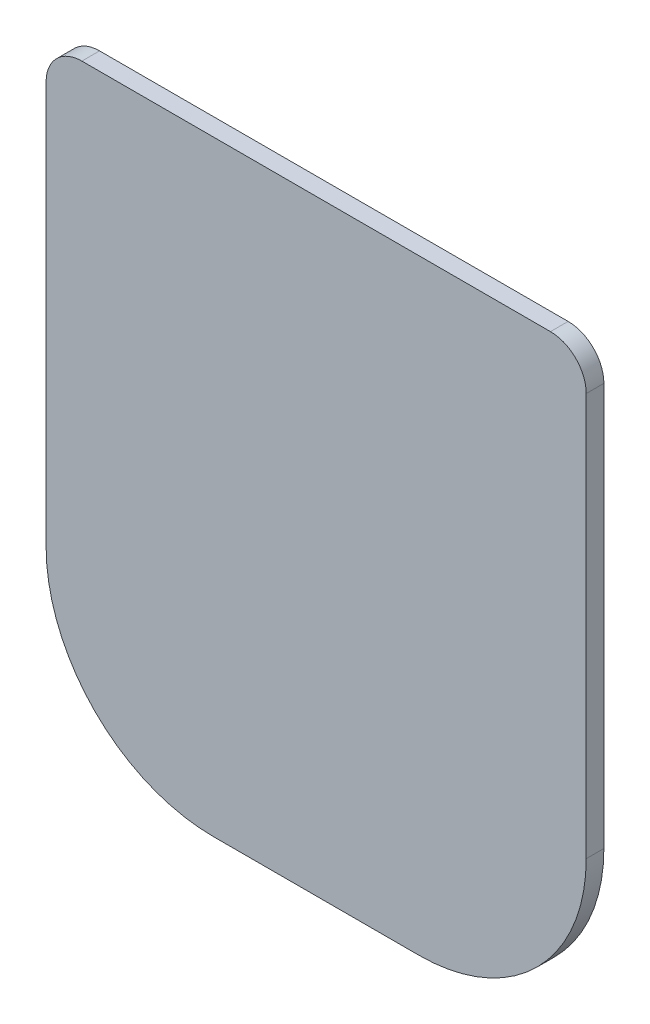
SolidWorks part; units mm, degrees
ref_plane "Front Plane" through (0, 0, 0) normal (0, 0, 1) x (1, 0, 0)
ref_plane "Top Plane" through (0, 0, 0) normal (0, 1, 0) x (1, 0, 0)
ref_plane "Right Plane" through (0, 0, 0) normal (1, 0, 0) x (0, 0, -1)
sketch "Sketch1" plane through (0, 0, 0) normal (0, 0, 1) x (1, 0, 0)
  line L0 (70, -39.19) -> (70, 58.81) construction
  line L1 (-25, -84.19) -> (-0.5, -84.19) construction
  line L2 (0.5, -84.19) -> (25, -84.19) construction
  line L3 (57, 71.81) -> (-57, 71.81) construction
  line L4 (70, 58.81) -> (-70, 58.81) construction
  line L5 (-70, 58.81) -> (-70, -39.19) construction
  line L6 (-0.5, -84.19) -> (0.5, -84.19) construction
  line L7 (-65.7, 58.81) -> (-65.7, -39.19)
  line L8 (-25, -79.89) -> (-0.5, -79.89)
  line L9 (-0.5, -79.89) -> (0.5, -79.89)
  line L10 (0.5, -79.89) -> (25, -79.89)
  line L11 (65.7, -39.19) -> (65.7, 58.81)
  line L12 (57, 67.51) -> (-57, 67.51)
  arc A0 (25, -84.19) -> (70, -39.19) centre (25, -39.19) ccw construction
  arc A1 (-70, -39.19) -> (-25, -84.19) centre (-25, -39.19) ccw construction
  arc A2 (70, 58.81) -> (57, 71.81) centre (57, 58.81) ccw construction
  arc A3 (-70, 58.81) -> (-57, 71.81) centre (-57, 58.81) cw construction
  arc A4 (-65.7, -39.19) -> (-25, -79.89) centre (-25, -39.19) ccw
  arc A5 (25, -79.89) -> (65.7, -39.19) centre (25, -39.19) ccw
  arc A6 (65.7, 58.81) -> (57, 67.51) centre (57, 58.81) ccw
  arc A7 (-65.7, 58.81) -> (-57, 67.51) centre (-57, 58.81) cw
  point P14 (0, 71.81)
  dimension "D1" = 13
  dimension "D2" = 98
  dimension "D3" = 4.3
  dimension "D4" = 156
  dimension "D5" = 71.81
  dimension "D6" = 140
extrude "Boss-Extrude1" add sketch "Sketch1" along normal blind 4.3
